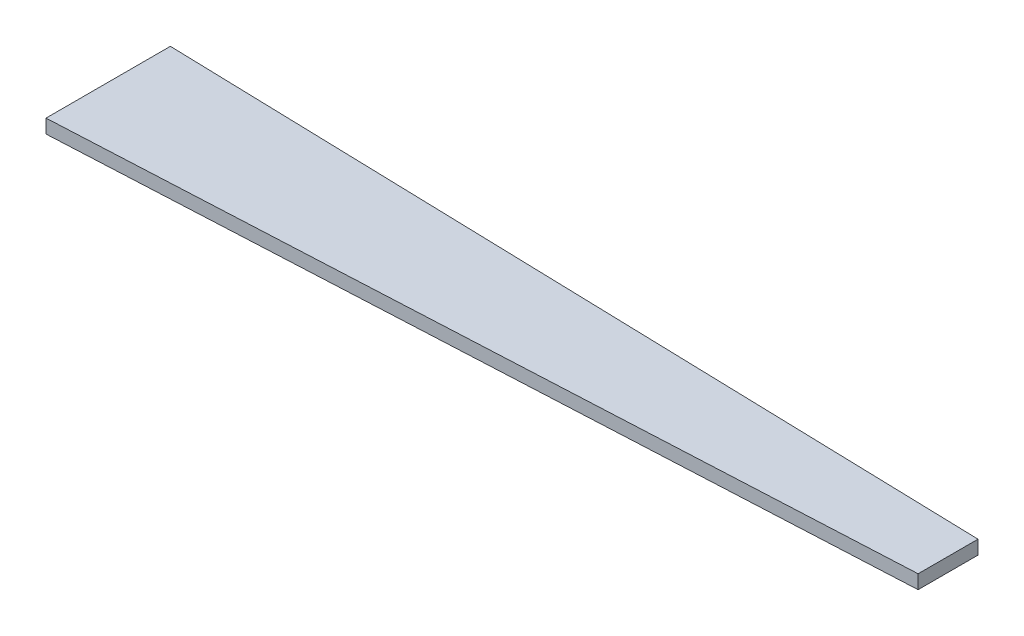
SolidWorks part; units mm, degrees
ref_plane "Ebene vorne" through (0, 0, 0) normal (0, 0, 1) x (1, 0, 0)
ref_plane "Ebene oben" through (0, 0, 0) normal (0, 1, 0) x (1, 0, 0)
ref_plane "Ebene rechts" through (0, 0, 0) normal (1, 0, 0) x (0, 0, -1)
sketch "Skizze1" plane through (0, 0, 0) normal (0, 0, 1) x (1, 0, 0)
  line L0 (0, 0) -> (400.8176, 6.9963)
  line L1 (400.8176, 6.9963) -> (1052.733, 52.5827)
  line L2 (1052.733, 52.5827) -> (1796.9249, 183.8038)
  line L3 (0, 0) -> (1940.6125, 0) construction
  dimension "D1" = 400.8176
  dimension "D2" = 1
  dimension "D3" = 4
  dimension "D4" = 10
  dimension "D5" = 651.9154
  dimension "D6" = 755.6723
  dimension "D7" = 1940.6125
sketch "Skizze2" plane through (0, 0, 0) normal (0, 1, 0) x (1, 0, 0)
  line L0 (0, 0) -> (0, -270)
  line L2 (0, 0) -> (1803.2172, -50)
  line L4 (1803.2172, -50) -> (1803.2172, -180)
  line L6 (1803.2172, -180) -> (0, -270)
  dimension "D1" = 270
  dimension "D2" = 1803.2172
  dimension "D3" = 130
  dimension "D4" = 50
extrude "Aufsatz-Linear austragen1" add sketch "Skizze2" along normal blind 30 contours L0 L6 L4 L2
